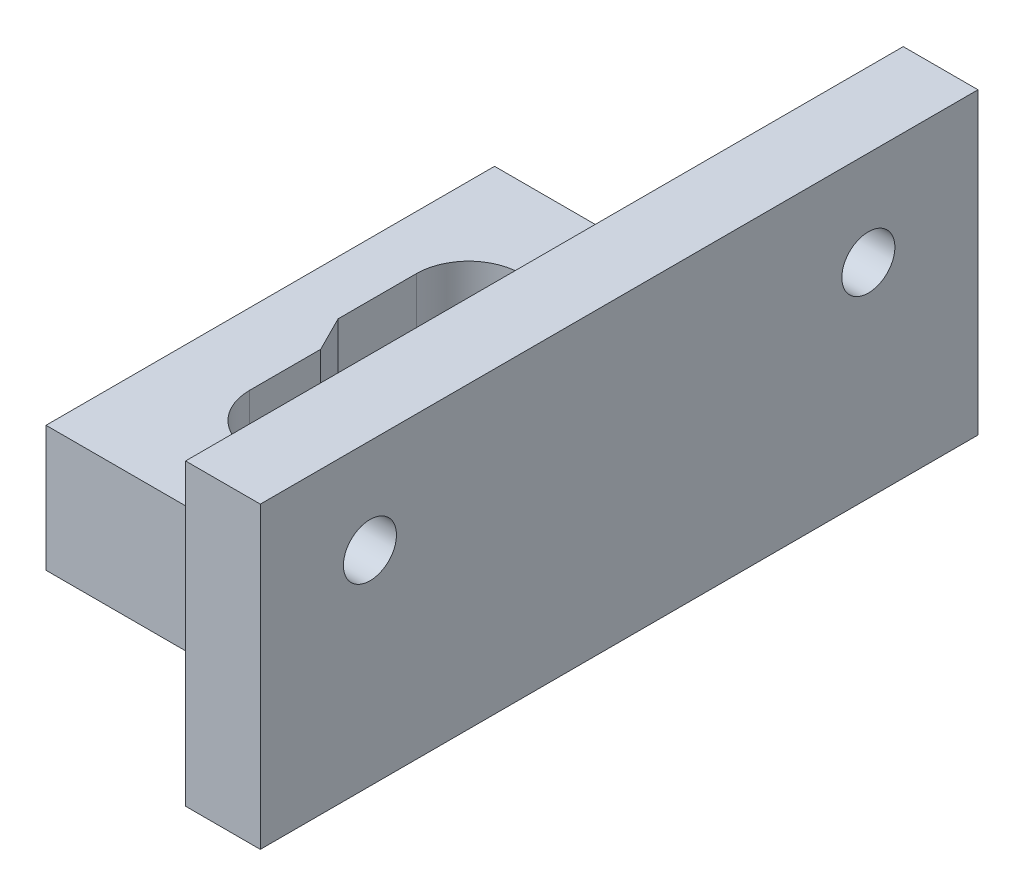
SolidWorks part; units mm, degrees
ref_plane "Front Plane" through (0, 0, 0) normal (0, 0, 1) x (1, 0, 0)
ref_plane "Top Plane" through (0, 0, 0) normal (0, 1, 0) x (1, 0, 0)
ref_plane "Right Plane" through (0, 0, 0) normal (1, 0, 0) x (0, 0, -1)
sketch "Sketch1" plane through (0, 0, 0) normal (0, 1, 0) x (1, 0, 0)
  line L0 (0, 0) -> (0, 11.43) construction
  line L1 (2.2087, 6.604) -> (-2.2087, 6.604)
  line L2 (0, 0) -> (13.208, 0) construction
  line L3 (-4.1137, 4.699) -> (-4.1137, 0.8928)
  line L4 (0, 0) -> (0, -13.208) construction
  line L5 (0, -6.604) -> (-1.3081, -6.604)
  line L6 (-3.2131, -4.699) -> (-3.2131, -0.8928)
  line L7 (-4.1137, 0.8928) -> (-3.2131, -0.8928)
  line L8 (4.1137, 0.8928) -> (3.2131, -0.8928)
  line L9 (4.1137, 4.699) -> (4.1137, 0.8928)
  line L10 (3.2131, -4.699) -> (3.2131, -0.8928)
  line L11 (0, -6.604) -> (1.3081, -6.604)
  line L12 (-7.62, 11.43) -> (7.62, 11.43)
  line L13 (7.62, 11.43) -> (7.62, -11.43)
  line L14 (7.62, -11.43) -> (-7.62, -11.43)
  line L15 (-7.62, 11.43) -> (-7.62, -11.43)
  arc A1 (-2.2087, 6.604) -> (-4.1137, 4.699) centre (-2.2087, 4.699) ccw
  arc A2 (-1.3081, -6.604) -> (-3.2131, -4.699) centre (-1.3081, -4.699) cw
  arc A3 (2.2087, 6.604) -> (4.1137, 4.699) centre (2.2087, 4.699) cw
  arc A4 (1.3081, -6.604) -> (3.2131, -4.699) centre (1.3081, -4.699) ccw
  point P17 (0, 5.715)
  point P27 (0, -11.43)
  dimension "D3" = 1.905
  dimension "D4" = 1.905
  dimension "D5" = 7.62
  dimension "D1" = 6.604
  dimension "D2" = 6.604
  dimension "D6" = 11.43
  dimension "D7" = 11.43
extrude "Boss-Extrude2" add sketch "Sketch1" along normal blind 6.4008
sketch "Sketch5" plane through (0, 6.4008, 0) normal (0, 1, 0) x (1, 0, 0)
  line L0 (0, 0) -> (11.1665, 0) construction
  line L1 (0, 0) -> (0, 11.43) construction
  line L2 (6.858, -8.128) -> (6.858, 8.128)
  line L3 (-6.858, 8.128) -> (6.858, 8.128)
  line L4 (-6.858, -8.128) -> (-6.858, 8.128)
  line L5 (-7.62, 11.43) -> (7.62, 11.43)
  line L6 (-7.62, 11.43) -> (-7.62, -11.43)
  line L7 (-7.62, -11.43) -> (7.62, -11.43)
  line L8 (7.62, 11.43) -> (7.62, -11.43)
  line L9 (-6.858, -8.128) -> (6.858, -8.128)
  point P13 (0, -8.128)
  point P14 (0, 8.128)
  point P16 (6.858, 0)
  point P17 (-6.858, 0)
sketch "Sketch6" plane through (0, 6.4008, 0) normal (0, 1, 0) x (1, 0, 0)
  line L0 (-3.2131, -0.8928) -> (-3.2131, -4.699) construction
  line L1 (-1.3081, -6.604) -> (1.3081, -6.604) construction
  line L2 (3.2131, -4.699) -> (3.2131, -0.8928) construction
  line L3 (3.2131, -0.8928) -> (4.1137, 0.8928) construction
  line L4 (4.1137, 0.8928) -> (4.1137, 4.699) construction
  line L5 (2.2087, 6.604) -> (-2.2087, 6.604) construction
  line L6 (-4.1137, 4.699) -> (-4.1137, 0.8928) construction
  line L7 (-4.1137, 0.8928) -> (-3.2131, -0.8928) construction
  line L8 (-3.2131, -0.8928) -> (-3.2131, -4.699) construction
  line L9 (-1.3081, -6.604) -> (1.3081, -6.604) construction
  line L10 (3.2131, -4.699) -> (3.2131, -0.8928) construction
  line L11 (3.2131, -0.8928) -> (4.1137, 0.8928) construction
  line L12 (4.1137, 0.8928) -> (4.1137, 4.699) construction
  line L13 (2.2087, 6.604) -> (-2.2087, 6.604) construction
  line L14 (-4.1137, 4.699) -> (-4.1137, 0.8928) construction
  line L15 (-4.1137, 0.8928) -> (-3.2131, -0.8928) construction
  line L16 (-3.9751, -1.0741) -> (-3.9751, -4.699)
  line L17 (-1.3081, -7.366) -> (1.3081, -7.366)
  line L18 (3.9751, -4.699) -> (3.9751, -1.0741)
  line L19 (3.9751, -1.0741) -> (4.8757, 0.7115)
  line L20 (4.8757, 0.7115) -> (4.8757, 4.699)
  line L21 (2.2087, 7.366) -> (-2.2087, 7.366)
  line L22 (-4.8757, 4.699) -> (-4.8757, 0.7115)
  line L23 (-4.8757, 0.7115) -> (-3.9751, -1.0741)
  arc A0 (-3.2131, -4.699) -> (-1.3081, -6.604) centre (-1.3081, -4.699) ccw construction
  arc A1 (1.3081, -6.604) -> (3.2131, -4.699) centre (1.3081, -4.699) ccw construction
  arc A2 (4.1137, 4.699) -> (2.2087, 6.604) centre (2.2087, 4.699) ccw construction
  arc A3 (-2.2087, 6.604) -> (-4.1137, 4.699) centre (-2.2087, 4.699) ccw construction
  arc A4 (-3.2131, -4.699) -> (-1.3081, -6.604) centre (-1.3081, -4.699) ccw construction
  arc A5 (1.3081, -6.604) -> (3.2131, -4.699) centre (1.3081, -4.699) ccw construction
  arc A6 (4.1137, 4.699) -> (2.2087, 6.604) centre (2.2087, 4.699) ccw construction
  arc A7 (-2.2087, 6.604) -> (-4.1137, 4.699) centre (-2.2087, 4.699) ccw construction
  arc A8 (-3.9751, -4.699) -> (-1.3081, -7.366) centre (-1.3081, -4.699) ccw
  arc A9 (1.3081, -7.366) -> (3.9751, -4.699) centre (1.3081, -4.699) ccw
  arc A10 (4.8757, 4.699) -> (2.2087, 7.366) centre (2.2087, 4.699) ccw
  arc A11 (-2.2087, 7.366) -> (-4.8757, 4.699) centre (-2.2087, 4.699) ccw
  dimension "D1" = 0.762
extrude "Cut-Extrude4" cut sketch "Sketch6" against normal through all both and the other way through all
ref_plane "Plane1" through (6.35, 0, 0) normal (1, 0, 0) x (0, 0, -1)
sketch "Sketch7" plane through (6.35, 0, 0) normal (1, 0, 0) x (0, 0, -1)
  line L1 (-18.288, 0) -> (18.288, 0)
  line L2 (-18.288, 0) -> (-18.288, 15.24)
  line L3 (-18.288, 15.24) -> (18.288, 15.24)
  line L4 (18.288, 0) -> (18.288, 15.24)
  line L5 (-11.43, 0) -> (11.43, 0) construction
  line L6 (11.43, 6.4008) -> (11.43, 0) construction
  line L7 (-11.43, 6.4008) -> (-11.43, 0) construction
  point P9 (11.43, 3.2004)
  point P10 (-18.288, 7.62)
  dimension "D1" = 15.24
  dimension "D2" = 6.858
  dimension "D3" = 6.858
extrude "Boss-Extrude3" add sketch "Sketch7" along normal blind 3.81 contours L2 L3 L4 L1
hole_wizard "#6-32 Tapped Hole1" positions "Sketch8" profile "Sketch9" tap size "#6-32" standard "ANSI Inch" end condition through all
sketch "Sketch8" plane through (6.35, 0, 0) normal (-1, 0, 0) x (0, 0, 1)
  line L5 (0, 15.24) -> (0, 2.9951) construction
  line L6 (18.288, 15.24) -> (-18.288, 15.24) construction
  line L8 (18.288, 15.24) -> (-18.288, 15.24) construction
  point P0 (12.7, 10.414)
  point P2 (-12.7, 10.414)
  dimension "D1" = 12.7
  dimension "D2" = 12.7
  dimension "D3" = 4.826
  dimension "D4" = 4.826
sketch "Sketch9" plane through (6.35, 10.414, 12.7) normal (0, 1, 0) x (0, 0, 1)
  line L0 (0, 0) -> (0, 3.81)
  line L1 (0, 3.81) -> (1.3525, 3.81)
  line L2 (1.3525, 3.81) -> (1.3525, 0.8685)
  line L3 (1.3525, 0.8685) -> (2.3876, 0)
  line L5 (2.3876, 0) -> (0, 0)
  line L6 (-1.3525, 0.8685) -> (-2.3876, 0) construction
  line L11 (0, -6.35) -> (0, 107.95) construction
  dimension "Thread Major Dia." = 2.7051
  dimension "Thru Tap Drill Depth" = 3.81
  dimension "Near C'Sink Dia." = 4.7752
  dimension "Near C'Sink Angle" = 100
